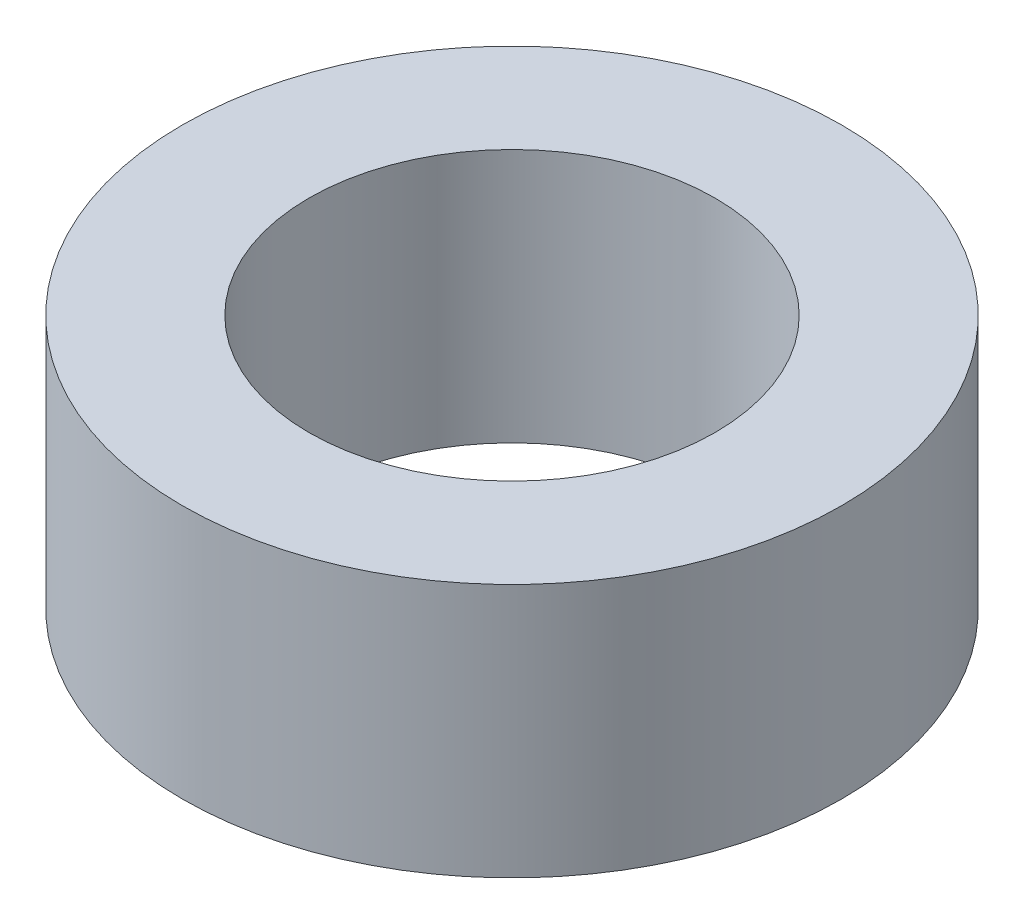
SolidWorks part; units mm, degrees
ref_plane "Front Plane" through (0, 0, 0) normal (0, 0, 1) x (1, 0, 0)
ref_plane "Top Plane" through (0, 0, 0) normal (0, 1, 0) x (1, 0, 0)
ref_plane "Right Plane" through (0, 0, 0) normal (1, 0, 0) x (0, 0, -1)
sketch "Sketch1" plane through (0, 0, 0) normal (0, 1, 0) x (1, 0, 0)
  circle A0 centre (0, 0) radius 2.9337
  circle A1 centre (0, 0) radius 4.7625
  dimension "D1" = 5.8674
  dimension "D2" = 9.525
extrude "Boss-Extrude1" add sketch "Sketch1" along normal blind 3.6703
